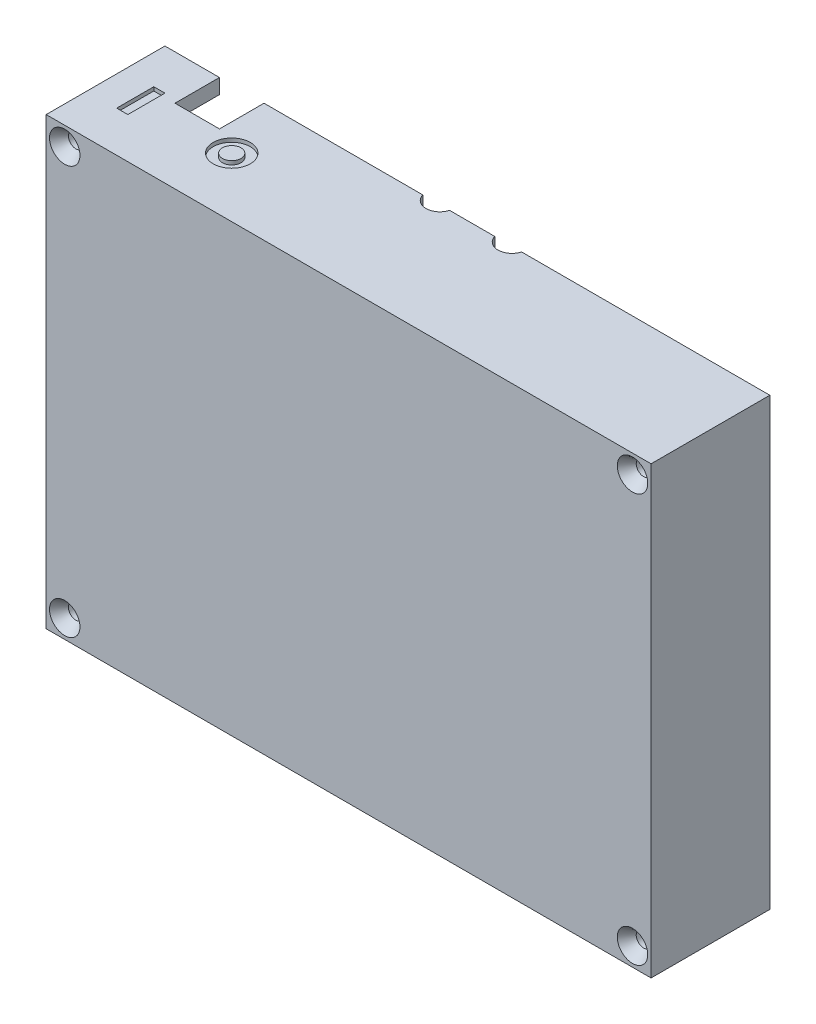
SolidWorks part; units mm, degrees
ref_plane "Front Plane" through (0, 0, 0) normal (0, 0, 1) x (1, 0, 0)
ref_plane "Top Plane" through (0, 0, 0) normal (0, 1, 0) x (1, 0, 0)
ref_plane "Right Plane" through (0, 0, 0) normal (1, 0, 0) x (0, 0, -1)
sketch "Sketch1" plane through (0, 0, 0) normal (0, 0, 1) x (1, 0, 0)
  line L0 (2.5, 27) -> (2.5, -27) construction
  line L6 (43.25, 29) -> (9.8071, 29) construction
  line L7 (43.25, -31) -> (43.25, 29) construction
  line L8 (-38.25, -31) -> (43.25, -31) construction
  line L9 (-38.25, -31) -> (-38.25, 29)
  line L10 (-36.25, -27) -> (-36.25, 24.25)
  line L11 (-38.25, -22.2205) -> (-38.25, -31) construction
  line L12 (-36.25, -21.2113) -> (-36.25, -24) construction
  line L14 (41.25, -24) -> (41.25, 24.25) construction
  line L15 (43.25, 29) -> (-38.25, 29)
  line L16 (43.25, -31) -> (43.25, 29)
  line L17 (-38.25, -31) -> (43.25, -31)
  line L24 (38.5, 27) -> (9.8071, 27) construction
  line L26 (-33.25, -27) -> (38.25, -27) construction
  line L33 (38.5, 27) -> (-33.5, 27)
  line L34 (41.25, -27) -> (41.25, 24.25)
  line L35 (-36.25, -27) -> (41.25, -27)
  arc A0 (-36.25, 24.25) -> (-33.5, 27) centre (-35.986, 26.736) ccw
  arc A1 (41.25, 24.25) -> (38.5, 27) centre (40.986, 26.736) cw
  dimension "D3" = 2.5
  dimension "D1" = 2.75
  dimension "D2" = 2.75
extrude "Boss-Extrude1" add sketch "Sketch1" along normal blind 14
sketch "Sketch3" plane through (0, 0, 14) normal (0, 0, 1) x (1, 0, 0)
  line L4 (-38.25, -31) -> (43.25, -31)
  line L5 (43.25, -31) -> (43.25, 29)
  line L6 (43.25, 29) -> (-38.25, 29)
  line L7 (-38.25, 29) -> (-38.25, -31)
  line L8 (-38.25, -31) -> (43.25, -31)
  line L9 (43.25, -31) -> (43.25, 29)
  line L10 (43.25, 29) -> (-38.25, 29)
  line L11 (-38.25, 29) -> (-38.25, -31)
  dimension "D1" = 0
extrude "Boss-Extrude2" add sketch "Sketch3" along normal blind 2
sketch "Sketch4" plane through (-38.25, 0, 0) normal (-1, 0, 0) x (0, 0, 1)
  circle A0 centre (0.5, -18) radius 3.25
  circle A1 centre (0.5, -2) radius 3.25
  circle A2 centre (0.5, 14) radius 3.25
  arc A5 (0, 1.2113) -> (0, -5.2113) centre (0.5, -2) ccw construction
  dimension "D1" = 6.5
extrude "Cut-Extrude1" cut sketch "Sketch4" against normal blind 2
sketch "Sketch5" plane through (0, 29, 0) normal (0, 1, 0) x (1, 0, 0)
  circle A0 centre (8, 0.5) radius 1.875
  circle A1 centre (-1.7, 0.5) radius 1.875
  circle A2 centre (-1.7, 0.5) radius 1.875 construction
  circle A3 centre (8, 0.5) radius 1.875 construction
extrude "Cut-Extrude2" cut sketch "Sketch5" against normal blind 2
sketch "Sketch6" plane through (0, 0, 14) normal (0, 0, -1) x (-1, 0, 0)
  line L0 (-38.5, 27) -> (-9.8071, 27) construction
  line L1 (-31, -24.25) -> (-31, -27)
  line L2 (-41.25, -27) -> (-41.25, 24.25) construction
  line L3 (-16.5, -23.25) -> (-16.5, 21.75) construction
  line L4 (0, -27) -> (0, 0) construction
  line L6 (-40.25, -26) -> (-40.25, 24.5) construction
  line L7 (36.25, -27) -> (-41.25, -27) construction
  line L8 (-31, -27) -> (-41.25, -27)
  line L9 (-41.25, -27) -> (-41.25, -21.75)
  line L10 (-41.25, -21.75) -> (-33.5, -21.75)
  line L11 (-41.25, 19.25) -> (-33.5, 19.25)
  line L12 (-31, 21.75) -> (-31, 27)
  line L13 (-41.25, 19.25) -> (-41.25, 27)
  line L14 (-41.25, 27) -> (-31, 27)
  line L15 (-43.25, -31) -> (-43.25, 29) construction
  circle A0 centre (-16.5, -23.25) radius 2.5 construction
  arc A1 (-31, -24.25) -> (-33.5, -21.75) centre (-33.5, -24.25) ccw
  circle A2 centre (-16.5, 21.75) radius 2.5 construction
  arc A3 (-33.5, 19.25) -> (-31, 21.75) centre (-33.5, 21.75) ccw
  circle A4 centre (-16.5, -23.25) radius 0.9 construction
  circle A5 centre (-33.5, -24.25) radius 0.9
  circle A6 centre (-16.5, 21.75) radius 0.9 construction
  circle A7 centre (-33.5, 21.75) radius 0.9
  point P12 (-16.5, -0.75)
  point P20 (-31, -25.625)
  point P24 (-40.25, -0.75)
  dimension "D1" = 1.8
  dimension "D5" = 5
  dimension "D9" = 2.5
  dimension "D10" = 2.5
  dimension "D2" = 5.25
  dimension "D3" = 17
  dimension "D4" = 7.75
  dimension "D6" = 7.75
  dimension "D7" = 12.25
  dimension "D8" = 10.25
extrude "Boss-Extrude3" add sketch "Sketch6" along normal blind 9
sketch "Sketch7" plane through (0, 0, 14) normal (0, 0, -1) x (-1, 0, 0)
  line L0 (-31, 27) -> (33.5, 27) construction
  line L1 (36.25, -27) -> (34.25, -27)
  line L2 (36.25, -27) -> (36.25, 27)
  line L3 (36.25, 27) -> (33.25, 27)
  line L4 (34.25, -27) -> (34.25, 24)
  line L5 (34.25, 24) -> (33.25, 24)
  line L6 (33.25, 24) -> (33.25, 27)
  line L7 (3.5071, 27) -> (33.5, 27) construction
  dimension "D1" = 2
  dimension "D2" = 3
  dimension "D3" = 3
extrude "Boss-Extrude4" add sketch "Sketch7" along normal blind 9
fillet "Fillet1" radius 3 2 edges at (41.25, -27, 2.5) (-36.25, -27, 2.5)
sketch "Sketch9" plane through (0, 0, 0) normal (0, 0, -1) x (-1, 0, 0)
  line L0 (0, -31) -> (0, 0) construction
  line L1 (38.25, -31) -> (-43.25, -31) construction
  line L2 (0, 0) -> (38.25, 0) construction
  line L3 (38.25, -5.25) -> (38.25, 1.25) construction
  line L4 (38.25, -21.2113) -> (38.25, -31) construction
  line L7 (38.25, 29) -> (38.25, -31) construction
  line L8 (-43.25, -31) -> (-43.25, 29) construction
  line L9 (-43.25, 29) -> (38.25, 29) construction
  circle A0 centre (35.75, -28.5) radius 1
  circle A1 centre (-40.75, -28.5) radius 1
  circle A2 centre (-40.75, 26.5) radius 1
  circle A3 centre (35.75, 26.5) radius 1
  dimension "D1" = 2
  dimension "D6" = 2
  dimension "D7" = 2
  dimension "D10" = 2
  dimension "D2" = 2.5
  dimension "D3" = 2.5
  dimension "D4" = 2.5
  dimension "D5" = 2.5
  dimension "D8" = 2.5
  dimension "D9" = 2.5
extrude "Cut-Extrude3" cut sketch "Sketch9" against normal through all
chamfer "Chamfer1" distance 1.5 angle 35 4 edges at (-36.75, -28.5, 16) (41.75, -28.5, 16) (39.75, 26.5, 16) (-34.75, 26.5, 16)
sketch "Sketch10" plane through (0, 29, 0) normal (0, 1, 0) x (1, 0, 0)
  line L0 (-3.5071, 0) -> (-38.25, 0) construction
  line L1 (-30.9, 0) -> (-24.9, 0)
  line L2 (-30.9, 0) -> (-30.9, -6)
  line L3 (-30.9, -6) -> (-24.9, -6)
  line L4 (-24.9, 0) -> (-24.9, -6)
  dimension "D1" = 6
  dimension "D2" = 5.35
  dimension "D3" = 6
extrude "Cut-Extrude4" cut sketch "Sketch10" against normal up to next
chamfer "Chamfer2" distance 1 angle 45 3 edges at (-38.25, 14, 3.75) (-38.25, -2, 3.75) (-38.25, -18, 3.75)
sketch "Sketch11" plane through (0, 29, 0) normal (0, 1, 0) x (1, 0, 0)
  line L0 (-34.25, -10.5) -> (-32.75, -10.5)
  line L1 (-34.25, -10.5) -> (-34.25, -5.5)
  line L2 (-34.25, -5.5) -> (-32.75, -5.5)
  line L3 (-32.75, -10.5) -> (-32.75, -5.5)
  line L4 (-30.9, 0) -> (-38.25, 0) construction
  line L5 (-38.25, -16) -> (-38.25, 0) construction
  circle A0 centre (-21.25, -8) radius 2.5
  circle A1 centre (-21.25, -8) radius 1.25
  point P7 (-34.25, -8)
  dimension "D4" = 5
  dimension "D5" = 2.5
  dimension "D1" = 8
  dimension "D2" = 4
  dimension "D3" = 17
  dimension "D6" = 5
  dimension "D7" = 1.5
extrude "Cut-Extrude5" cut sketch "Sketch11" against normal blind 0.5
